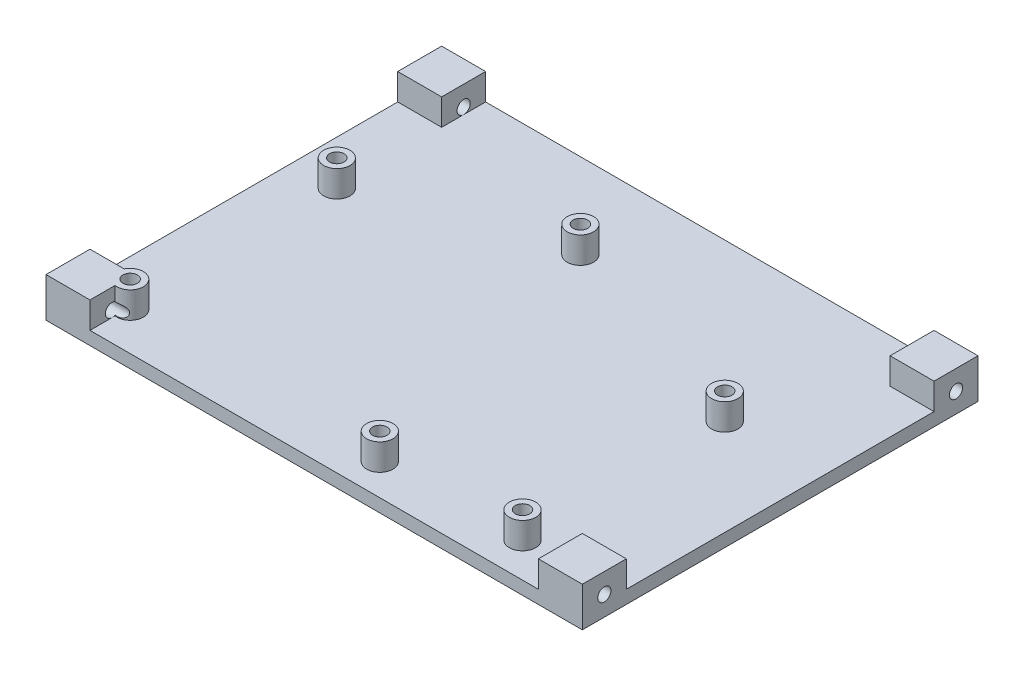
SolidWorks part; units mm, degrees
ref_plane "Front Plane" through (0, 0, 0) normal (0, 0, 1) x (1, 0, 0)
ref_plane "Top Plane" through (0, 0, 0) normal (0, 1, 0) x (1, 0, 0)
ref_plane "Right Plane" through (0, 0, 0) normal (1, 0, 0) x (0, 0, -1)
sketch "Sketch1" plane through (0, 0, 0) normal (0, 1, 0) x (1, 0, 0)
  line L1 (0, 0) -> (122, 0)
  line L2 (0, 0) -> (0, 90)
  line L3 (0, 90) -> (122, 90)
  line L4 (122, 0) -> (122, 90)
  dimension "D1" = 122
  dimension "D2" = 90
extrude "Boss-Extrude1" add sketch "Sketch1" along normal blind 3
sketch "Sketch2" plane through (0, 3, 0) normal (0, 1, 0) x (1, 0, 0)
  line L0 (122, 90) -> (0, 90) construction
  line L1 (0, 0) -> (10, 0)
  line L2 (0, 0) -> (0, 10)
  line L3 (0, 10) -> (7.7811, 10)
  line L4 (10, 0) -> (10, 5.7066)
  line L5 (0, 90) -> (10, 90)
  line L6 (0, 90) -> (0, 80)
  line L7 (0, 80) -> (10, 80)
  line L8 (10, 90) -> (10, 80)
  line L9 (122, 90) -> (112, 90)
  line L10 (122, 90) -> (122, 80)
  line L11 (122, 80) -> (112, 80)
  line L12 (112, 90) -> (112, 80)
  line L13 (122, 0) -> (112, 0)
  line L14 (122, 0) -> (122, 10)
  line L15 (122, 10) -> (112, 10)
  line L16 (112, 0) -> (112, 10)
  line L18 (0, 90) -> (0, 0) construction
  circle A5 centre (68.8138, 7.1202) radius 3
  circle A6 centre (100.513, 7.8822) radius 3
  circle A7 centre (10.089, 56.0656) radius 3
  circle A8 centre (100.132, 54.2622) radius 3
  circle A9 centre (50.856, 70.696) radius 3
  arc A10 (10, 5.7066) -> (7.7811, 10) centre (10.47, 8.6696) ccw
  dimension "D3" = 6
  dimension "D4" = 6
  dimension "D5" = 6
  dimension "D6" = 6
  dimension "D7" = 6
  dimension "D8" = 10.089
  dimension "D9" = 47.396
  dimension "D18" = 0.762
  dimension "D19" = 31.6992
  dimension "D20" = 0.381
  dimension "D21" = 46.38
  dimension "D22" = 16.4338
  dimension "D23" = 49.276
  dimension "D24" = 14.6304
  dimension "D25" = 40.767
  dimension "D27" = 19.304
  dimension "D16" = 6
  dimension "D17" = 58.3438
  dimension "D10" = 10
  dimension "D11" = 10
  dimension "D12" = 10
  dimension "D13" = 10
  dimension "D14" = 10
  dimension "D15" = 10
extrude "Boss-Extrude2" add sketch "Sketch2" along normal blind 6
sketch "Sketch3" plane through (0, 9, 0) normal (0, 1, 0) x (1, 0, 0)
  circle A4 centre (10.089, 56.0656) radius 1.65
  circle A5 centre (50.856, 70.696) radius 1.65
  circle A6 centre (100.132, 54.2622) radius 1.65
  circle A7 centre (100.513, 7.8822) radius 1.65
  circle A8 centre (68.8138, 7.1202) radius 1.65
  circle A9 centre (10.47, 8.6696) radius 1.65
  dimension "D1" = 3.3
  dimension "D2" = 3.3
  dimension "D3" = 3.3
  dimension "D4" = 3.3
  dimension "D5" = 3.3
  dimension "D6" = 3.3
extrude "Cut-Extrude1" cut sketch "Sketch3" against normal blind 26
sketch "Sketch4" plane through (0, 0, 0) normal (-1, 0, 0) x (0, 0, 1)
  circle A0 centre (-85, 4.5) radius 1.5
  circle A1 centre (-5, 4.5) radius 1.5
  dimension "D1" = 3
  dimension "D2" = 3
extrude "Cut-Extrude2" cut sketch "Sketch4" against normal up to next
sketch "Sketch5" plane through (122, 0, 0) normal (1, 0, 0) x (0, 0, -1)
  circle A0 centre (85, 4.5) radius 1.5
  circle A1 centre (5, 4.5) radius 1.5
extrude "Cut-Extrude3" cut sketch "Sketch5" against normal up to next
